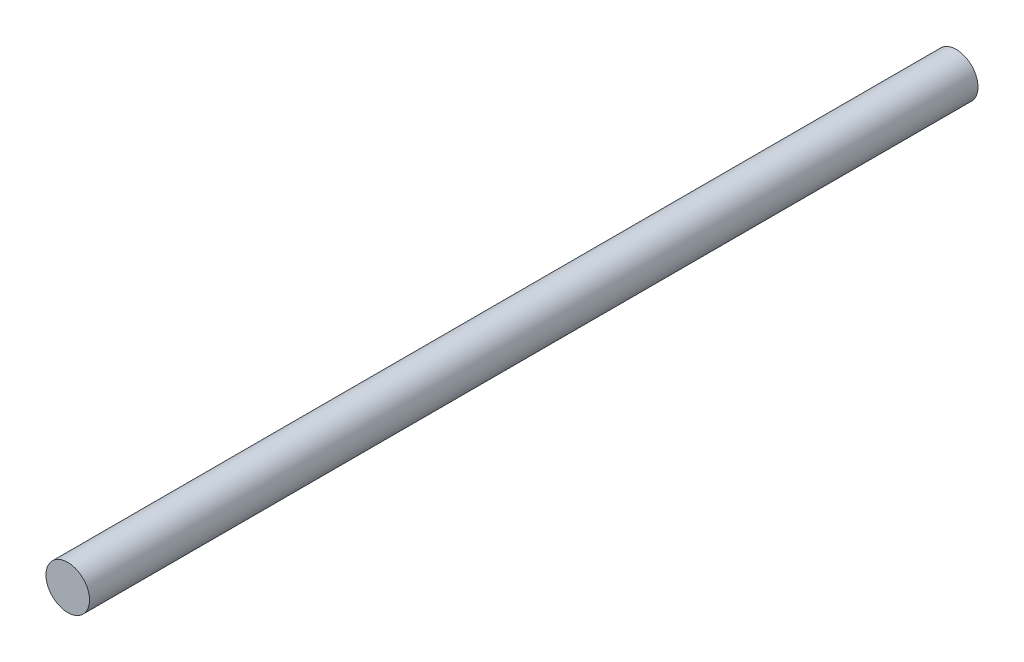
SolidWorks part; units mm, degrees
ref_plane "Front Plane" through (0, 0, 0) normal (0, 0, 1) x (1, 0, 0)
ref_plane "Top Plane" through (0, 0, 0) normal (0, 1, 0) x (1, 0, 0)
ref_plane "Right Plane" through (0, 0, 0) normal (1, 0, 0) x (0, 0, -1)
sketch "Sketch1" plane through (0, 0, 0) normal (0, 0, 1) x (1, 0, 0)
  circle A0 centre (0, 0) radius 2.5
  dimension "D1" = 5
extrude "Boss-Extrude1" add sketch "Sketch1" against normal blind 102
